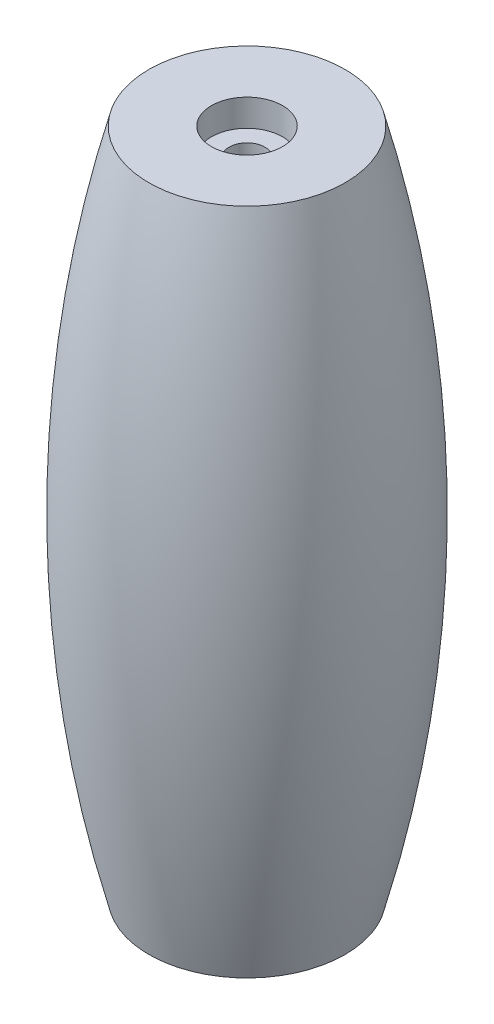
SolidWorks part; units mm, degrees
material "Natural Rubber"
ref_plane "Front Plane" through (0, 0, 0) normal (0, 0, 1) x (1, 0, 0)
ref_plane "Top Plane" through (0, 0, 0) normal (0, 1, 0) x (1, 0, 0)
ref_plane "Right Plane" through (0, 0, 0) normal (1, 0, 0) x (0, 0, -1)
sketch "Sketch1" plane through (0, 0, 0) normal (0, 0, 1) x (1, 0, 0)
  line L0 (169.7242, 39.8508) -> (522.3478, 39.8508) construction
sketch "Sketch4" plane through (0, 0, 0) normal (0, 0, 1) x (1, 0, 0)
  line L0 (-19.0897, 14.0809) -> (-12.1881, 14.0809)
  line L1 (-19.0897, -32.9191) -> (-12.1881, -32.9191)
  line L2 (-19.0897, 14.0809) -> (-19.0897, -32.9191)
  arc A0 (-12.1881, 14.0809) -> (-12.1881, -32.9191) centre (-100.9881, -9.4191) cw
revolve "Revolve2" add sketch "Sketch4" angle 360 about L2
sketch "Sketch7" plane through (0, 14.0809, 0) normal (0, 1, 0) x (1, 0, 0)
  circle A0 centre (-19.0897, 0) radius 1.25
  circle A1 centre (-19.0897, 0) radius 6.9016 construction
  dimension "D1" = 2.5
extrude "Cut-Extrude6" cut sketch "Sketch7" against normal through all
sketch "Sketch8" plane through (0, -32.9191, 0) normal (0, -1, 0) x (1, 0, 0)
  circle A0 centre (-19.0897, 0) radius 2.5
  dimension "D1" = 5
sketch "Sketch9" plane through (0, 14.0809, 0) normal (0, 1, 0) x (1, 0, 0)
  circle A0 centre (-19.0897, 0) radius 2.5 construction
  circle A1 centre (-19.0897, 0) radius 2.5
extrude "Cut-Extrude7" cut sketch "Sketch8" against normal blind 1.9 contours A0
extrude "Cut-Extrude8" cut sketch "Sketch9" against normal blind 1.9 contours A1
sketch "Sketch3" [suppressed] plane through (0, 0, 0) normal (0, 1, 0) x (1, 0, 0)
  circle A0 centre (-58.2912, 0) radius 1.25
  dimension "D1" = 2.5
scale "Scale1" scale about centroid uniform scaling yes scale factor 0.95
scale "Scale2" scale about centroid uniform scaling yes scale factor 1.052632
scale "Scale3" scale about centroid uniform scaling yes scale factor 0.94
equation "\"s\"= 2.5'shaft diameter"
equation "\"D1@Sketch3\"=\"s\""
equation "\"D1@Sketch7\"=\"s\""
equation "\"b\"= 5'bearing outer diameter"
equation "\"D1@Sketch8\"=\"b\""
equation "\"bh\"=1.9"
equation "\"D1@Cut-Extrude7\"=\"bh\""
equation "\"D1@Cut-Extrude8\"=\"bh\""
